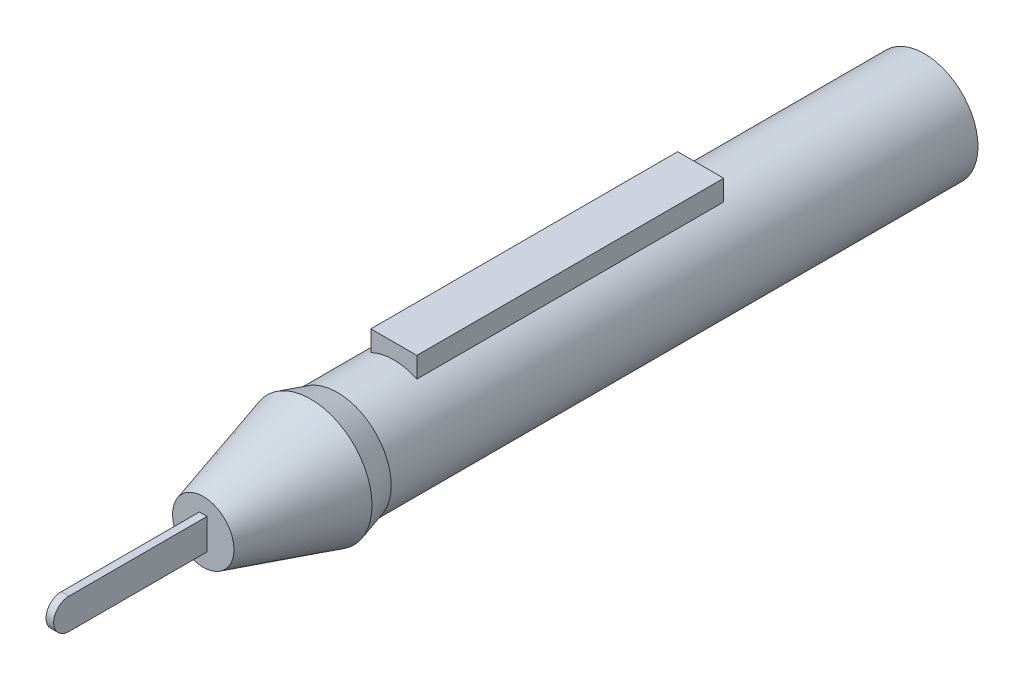
SolidWorks part; units mm, degrees
ref_plane "Front Plane" through (0, 0, 0) normal (0, 0, 1) x (1, 0, 0)
ref_plane "Top Plane" through (0, 0, 0) normal (0, 1, 0) x (1, 0, 0)
ref_plane "Right Plane" through (0, 0, 0) normal (1, 0, 0) x (0, 0, -1)
sketch "Sketch1" plane through (0, 0, 0) normal (1, 0, 0) x (0, 0, -1)
  line L0 (0, 0) -> (30.8864, 0) construction
  line L1 (0, 2) -> (0, -2) construction
  line L2 (0, 2) -> (30.1406, 2) construction
  line L3 (0, -2) -> (28.8712, -2) construction
  line L4 (2, 2) -> (20, 2)
  line L5 (2, -2) -> (20, -2)
  line L6 (20, 2) -> (20, -2)
  arc A0 (2, -2) -> (2, 2) centre (2, 0) cw
  point P5 (0, 0)
  dimension "D1" = 4
  dimension "D2" = 20
extrude "Boss-Extrude1" add sketch "Sketch1" along normal mid plane 1
sketch "Sketch2" plane through (0, 0, 0) normal (1, 0, 0) x (0, 0, -1)
  line L0 (20, 0) -> (34, 0) construction
  line L1 (20, -2) -> (20, 2) construction
  line L2 (20, 0) -> (20, 4)
  line L3 (20, 4) -> (34, 8)
  line L5 (34, 0) -> (20, 0)
  line L6 (34, 8) -> (37.4951, 6.9981)
  line L7 (37.4951, 6.9981) -> (114, 6.9981)
  line L8 (114, 6.9981) -> (114, 0)
  line L9 (114, 0) -> (34, 0)
  dimension "D1" = 14
  dimension "D2" = 4
  dimension "D3" = 8
  dimension "D4" = 80
revolve "Revolve1" add sketch "Sketch2" angle 360 about L0
sketch "Sketch3" plane through (0, 0, 0) normal (0, 1, 0) x (1, 0, 0)
  line L0 (0, 0) -> (0, 143.1933) construction
  line L1 (-3, 84.8473) -> (3, 84.8473)
  line L2 (-3, 84.8473) -> (-3, 44.8473)
  line L3 (-3, 44.8473) -> (3, 44.8473)
  line L4 (3, 84.8473) -> (3, 44.8473)
  point P7 (0, 44.8473)
  dimension "D1" = 6
  dimension "D2" = 40
extrude "Boss-Extrude2" add sketch "Sketch3" along normal blind 9
